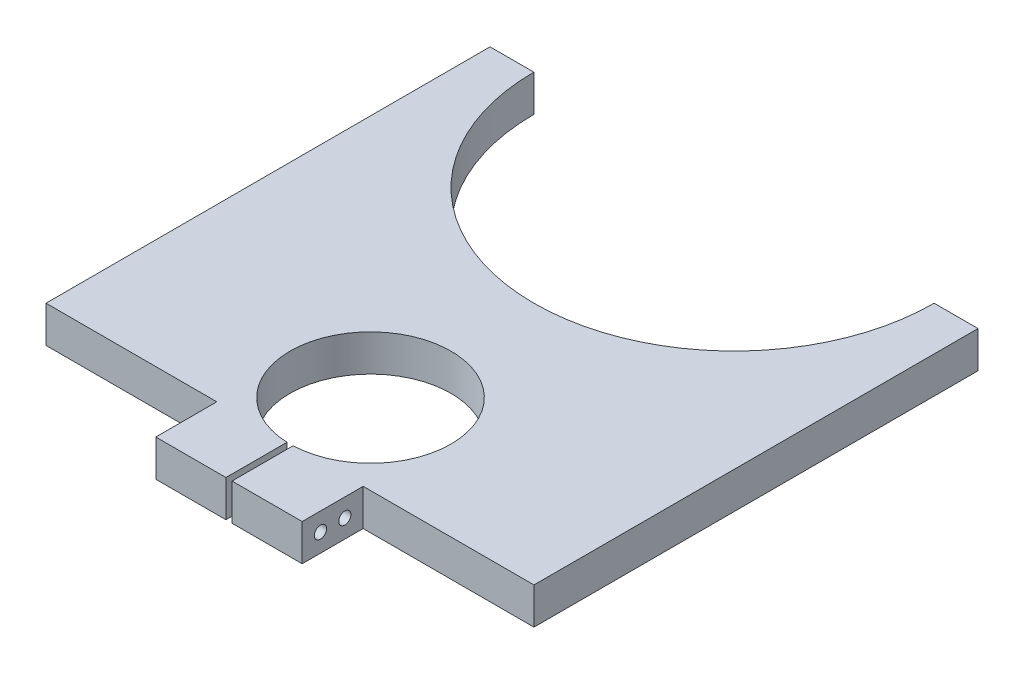
SolidWorks part; units mm, degrees
ref_plane "Front Plane" through (0, 0, 0) normal (0, 0, 1) x (1, 0, 0)
ref_plane "Top Plane" through (0, 0, 0) normal (0, 1, 0) x (1, 0, 0)
ref_plane "Right Plane" through (0, 0, 0) normal (1, 0, 0) x (0, 0, -1)
sketch "Sketch1" plane through (0, 0, 0) normal (0, 1, 0) x (1, 0, 0)
  line L0 (0, 0) -> (0, -131.445)
  line L1 (0, -131.445) -> (127, -131.445)
  line L2 (127, -131.445) -> (127, 0)
  line L3 (127, 0) -> (0, 0)
  dimension "D1" = 127
  dimension "D2" = 131.445
extrude "Boss-Extrude1" add sketch "Sketch1" along normal blind 9.525
sketch "Sketch2" plane through (0, 9.525, 0) normal (0, 1, 0) x (1, 0, 0)
  line L0 (0, -131.445) -> (44.45, -131.445)
  line L1 (0, -131.445) -> (127, -131.445) construction
  line L2 (127, -131.445) -> (82.55, -131.445)
  line L3 (44.45, -131.445) -> (44.45, -115.57)
  line L4 (44.45, -115.57) -> (0, -115.57)
  line L5 (0, 0) -> (0, -131.445) construction
  line L6 (0, -115.57) -> (0, -131.445)
  line L7 (82.55, -131.445) -> (82.55, -115.57)
  line L8 (82.55, -115.57) -> (127, -115.57)
  line L9 (127, -131.445) -> (127, 0) construction
  line L10 (127, -115.57) -> (127, -131.445)
  dimension "D1" = 44.45
  dimension "D2" = 44.45
  dimension "D3" = 15.875
extrude "Cut-Extrude1" cut sketch "Sketch2" against normal through all
sketch "Sketch3" plane through (0, 9.525, 0) normal (0, 1, 0) x (1, 0, 0)
  line L0 (63.5, -131.445) -> (64.2938, -131.445)
  line L1 (44.45, -131.445) -> (82.55, -131.445) construction
  line L2 (63.5, -131.445) -> (62.7063, -131.445)
  line L3 (62.7063, -131.445) -> (62.7063, -115.57)
  line L5 (64.2938, -115.57) -> (64.2938, -131.445)
  line L7 (64.2938, -115.57) -> (64.2938, -115.555)
  line L8 (62.7063, -115.57) -> (62.7063, -115.555)
  arc A0 (64.2938, -115.555) -> (62.7063, -115.555) centre (63.5, -94.615) ccw
  dimension "D1" = 0.7937
  dimension "D2" = 0.7937
extrude "Cut-Extrude2" cut sketch "Sketch3" against normal through all
sketch "Sketch5" plane through (0, 9.525, 0) normal (0, 1, 0) x (1, 0, 0)
  line L0 (127, 0) -> (0, 0)
  circle A0 centre (63.5, 0) radius 52.0852
  dimension "D1" = 104.1705
extrude "Cut-Extrude3" cut sketch "Sketch5" against normal through all contours L0 A0
sketch "Sketch6" plane through (44.45, 0, 0) normal (-1, 0, 0) x (0, 0, 1)
  line L0 (131.445, 0) -> (131.445, 9.525) construction
  circle A0 centre (120.3325, 4.7625) radius 1.5875
  circle A1 centre (126.6825, 4.7625) radius 1.5875
  dimension "D1" = 3.175
  dimension "D2" = 3.175
  dimension "D3" = 4.7625
  dimension "D4" = 11.1125
extrude "Cut-Extrude4" cut sketch "Sketch6" against normal through all
